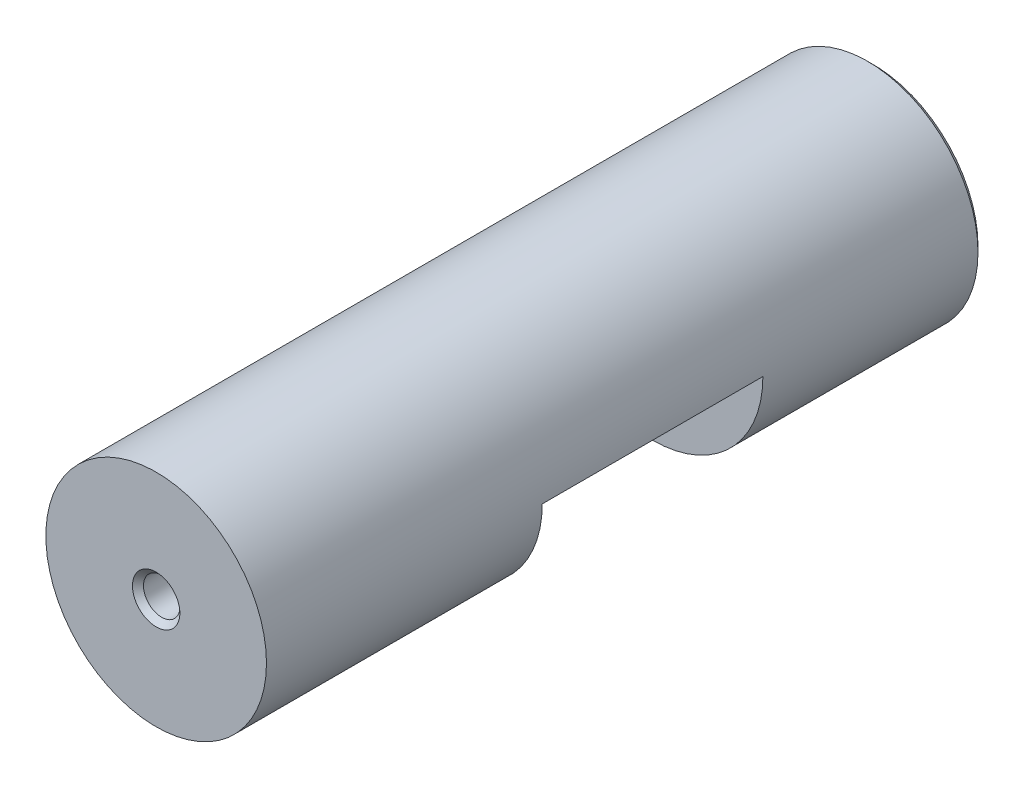
SolidWorks part; units mm, degrees
ref_plane "Front Plane" through (0, 0, 0) normal (0, 0, 1) x (1, 0, 0)
ref_plane "Top Plane" through (0, 0, 0) normal (0, 1, 0) x (1, 0, 0)
ref_plane "Right Plane" through (0, 0, 0) normal (1, 0, 0) x (0, 0, -1)
sketch "Sketch1" plane through (0, 0, 0) normal (0, 0, 1) x (1, 0, 0)
  circle A0 centre (0, 0) radius 10
  dimension "D1" = 20
extrude "Boss-Extrude1" add sketch "Sketch1" along normal blind 65
sketch "Sketch2" plane through (0, 0, 65) normal (0, 0, 1) x (1, 0, 0)
  circle A0 centre (0, 0) radius 1.65
  dimension "D1" = 3.3
extrude "Cut-Extrude1" cut sketch "Sketch2" against normal blind 15
chamfer "Chamfer1" distance 0.5 angle 45 1 edges at (1.65, 0, 65)
sketch "Sketch3" plane through (0, 0, 0) normal (0, 0, -1) x (-1, 0, 0)
  circle A0 centre (0, 0) radius 5
  dimension "D1" = 10
extrude "Cut-Extrude2" cut sketch "Sketch3" against normal blind 15
chamfer "Chamfer2" distance 0.5 angle 45 1 edges at (-5, 0, 0)
chamfer "Chamfer3" distance 0.5 angle 45 1 edges at (10, 0, 0)
sketch "Sketch4" plane through (0, 0, 0) normal (0, 1, 0) x (1, 0, 0)
  line L0 (9.5, 0) -> (-9.5, 0) construction
  line L1 (-12.1982, -20) -> (12.3501, -20)
  line L2 (-12.1982, -20) -> (-12.1982, -40)
  line L3 (-12.1982, -40) -> (12.3501, -40)
  line L4 (12.3501, -20) -> (12.3501, -40)
  dimension "D1" = 20
  dimension "D2" = 20
extrude "Cut-Extrude3" cut sketch "Sketch4" against normal blind 13
sketch "Sketch5" plane through (0, 0, 20) normal (0, 0, 1) x (1, 0, 0)
  line L0 (0, 0) -> (0, -15.5034) construction
